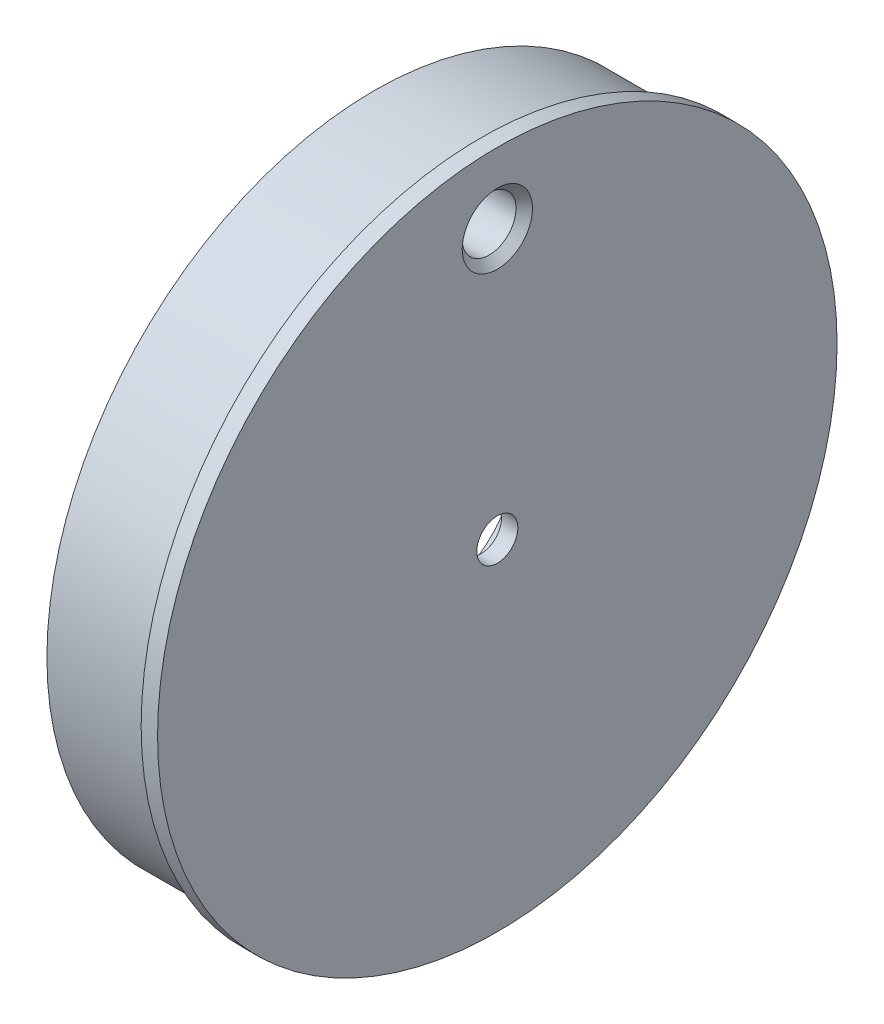
SolidWorks part; units mm, degrees
material "6061-T6 Al"
ref_plane "Front Plane" through (0, 0, 0) normal (0, 0, 1) x (1, 0, 0)
ref_plane "Top Plane" through (0, 0, 0) normal (0, 1, 0) x (1, 0, 0)
ref_plane "Right Plane" through (0, 0, 0) normal (1, 0, 0) x (0, 0, -1)
sketch "Sketch1" plane through (0, 0, 0) normal (0, 0, 1) x (1, 0, 0)
  line L0 (0, 0) -> (-9.525, 0) construction
  line L1 (0, 1.5875) -> (0, 26.289)
  line L2 (0, 26.289) -> (-1.27, 26.289)
  line L3 (-1.27, 26.289) -> (-1.27, 25.3238)
  line L4 (-1.27, 25.3238) -> (-9.525, 25.3238)
  line L5 (-9.525, 25.3238) -> (-9.525, 17.1958)
  line L6 (-9.525, 17.1958) -> (-6.223, 17.1958)
  line L7 (-1.27, 5.08) -> (-1.27, 1.5875)
  line L8 (-1.27, 1.5875) -> (0, 1.5875)
  line L10 (-4.953, 15.9258) -> (-4.953, 6.35)
  line L11 (-4.953, 6.35) -> (-2.54, 6.35)
  arc A0 (-2.54, 6.35) -> (-1.27, 5.08) centre (-2.54, 5.08) cw
  arc A1 (-6.223, 17.1958) -> (-4.953, 15.9258) centre (-6.223, 15.9258) cw
  dimension "D10" = 1.27
  dimension "D1" = 3.175
  dimension "D2" = 1.27
  dimension "D3" = 52.578
  dimension "D4" = 50.6476
  dimension "D5" = 34.3916
  dimension "D6" = 9.525
  dimension "D7" = 8.128
  dimension "D8" = 12.7
  dimension "D11" = 0.9652
  dimension "D12" = 4.572
revolve "Revolve1" add sketch "Sketch1" angle 360 about L0
hole_wizard "#8-32 Tapped Hole1" positions "Sketch4" profile "Sketch3" tap size "#8-32" standard "ANSI Inch" end condition through all
sketch "Sketch4" plane through (-9.525, 0, 0) normal (-1, 0, 0) x (0, 0, 1)
  circle A5 centre (0, 20.828) radius 3.3782 construction
  circle A6 centre (0, 20.828) radius 4.064 construction
  circle A7 centre (0, 0) radius 25.3238 construction
  point P12 (0, 20.828)
  dimension "D1" = 20.828
  dimension "D2" = 8.128
  dimension "D3" = 6.7564
  dimension "D4" = 0.4318
sketch "Sketch3" plane through (-9.525, 20.828, 0) normal (0, 1, 0) x (0, 0, 1)
  line L0 (0, 0) -> (0, 9.525)
  line L1 (0, 9.525) -> (2.7178, 9.525)
  line L2 (2.0828, 8.89) -> (2.0828, 0.635)
  line L3 (2.0828, 0.635) -> (2.7178, 0)
  line L5 (2.7178, 0) -> (0, 0)
  line L6 (-2.0828, 0.635) -> (-2.7178, 0) construction
  line L7 (2.7178, 9.525) -> (2.0828, 8.89)
  line L8 (-2.7178, 9.525) -> (-2.0828, 8.89) construction
  line L11 (0, -6.35) -> (0, 107.95) construction
  dimension "Thread Major Dia." = 4.1656
  dimension "Thru Tap Drill Depth" = 9.525
  dimension "Near C'Sink Dia." = 5.4356
  dimension "Near C'Sink Angle" = 90
  dimension "Far C'Sink Dia." = 5.4356
  dimension "Far C'Sink Angle" = 90
sketch "Sketch2" [suppressed] plane through (0, 0, 0) normal (0, 0, 1) x (1, 0, 0)
  line L0 (0, 0) -> (-9.525, 0) construction
  line L1 (0, 0) -> (-9.525, 0) construction
  line L3 (-4.953, 3.2258) -> (-4.953, 4.4958) construction
  line L4 (-4.953, 3.2258) -> (-4.953, 4.4958)
  line L5 (-4.953, 4.4958) -> (-6.223, 4.4958)
  arc A0 (-4.953, 3.2258) -> (-6.223, 4.4958) centre (-6.223, 3.2258) ccw construction
  arc A1 (-4.953, 3.2258) -> (-6.223, 4.4958) centre (-6.223, 3.2258) ccw
revolve "Cut-Revolve1" [suppressed] cut sketch "Sketch2" angle 360 about L1
